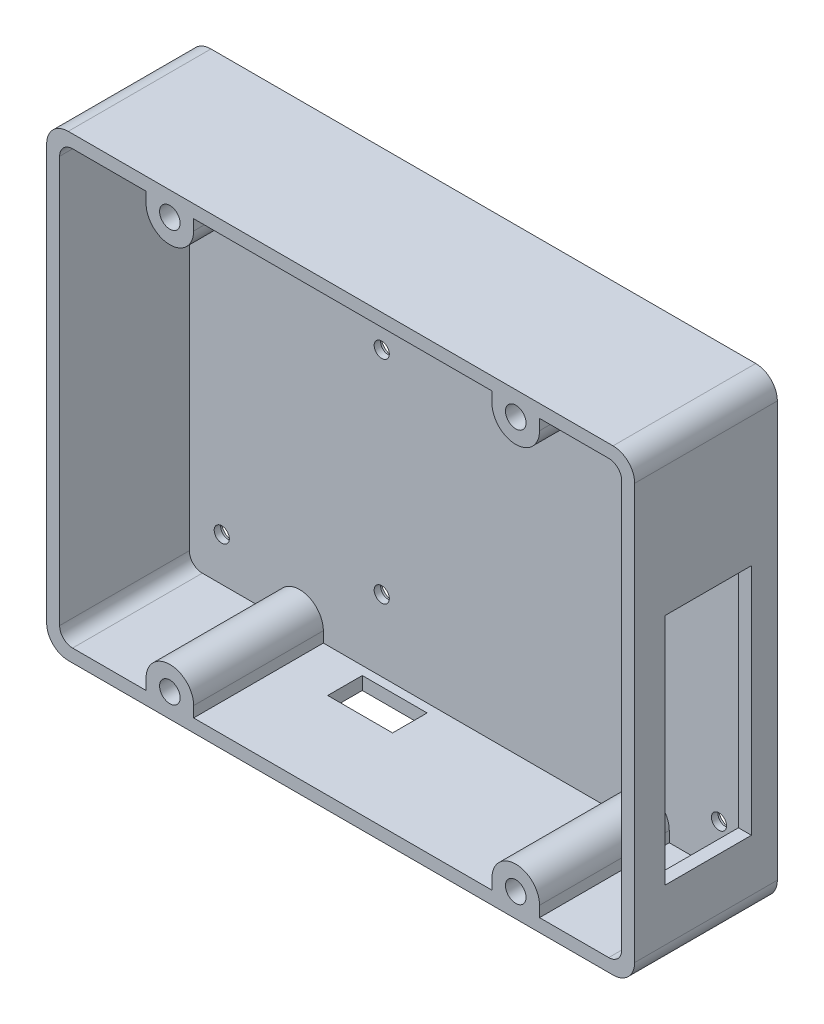
SolidWorks part; units mm, degrees
ref_plane "Plan de face" through (0, 0, 0) normal (0, 0, 1) x (1, 0, 0)
ref_plane "Plan de dessus" through (0, 0, 0) normal (0, 1, 0) x (1, 0, 0)
ref_plane "Plan de droite" through (0, 0, 0) normal (1, 0, 0) x (0, 0, -1)
sketch "Esquisse1" plane through (0, 0, 0) normal (0, 0, 1) x (1, 0, 0)
  line L0 (7.5, 10) -> (122.5, 10) construction
  line L1 (0, 0) -> (130, 0)
  line L2 (0, 0) -> (0, 100)
  line L3 (0, 100) -> (130, 100)
  line L4 (130, 0) -> (130, 100)
  line L5 (122.5, 10) -> (122.5, 94) construction
  line L6 (122.5, 94) -> (7.5, 94) construction
  line L7 (7.5, 94) -> (7.5, 10) construction
  line L8 (65, 40.971) -> (65, 68.9984) construction
  line L9 (44.5, 16.5) -> (102, 16.5) construction
  line L10 (102, 16.5) -> (102, 65.5) construction
  line L11 (102, 65.5) -> (44.5, 65.5) construction
  line L12 (44.5, 65.5) -> (44.5, 16.5) construction
  circle A0 centre (122.5, 10) radius 1.75
  circle A1 centre (122.5, 94) radius 1.75
  circle A2 centre (7.5, 94) radius 1.75
  circle A3 centre (7.5, 10) radius 1.75
  circle A4 centre (44.5, 65.5) radius 1.75
  circle A5 centre (102, 65.5) radius 1.75
  circle A6 centre (102, 16.5) radius 1.75
  circle A7 centre (44.5, 16.5) radius 1.75
  dimension "D5" = 3.5
  dimension "D1" = 100
  dimension "D2" = 130
  dimension "D3" = 115
  dimension "D4" = 84
  dimension "D6" = 6
  dimension "D7" = 57.5
  dimension "D8" = 49
  dimension "D9" = 20.5
  dimension "D10" = 6.5
extrude "Boss.-Extru.1" add sketch "Esquisse1" along normal blind 3
sketch "Esquisse2" plane through (0, 0, 0) normal (0, 0, -1) x (-1, 0, 0)
  circle A0 centre (-102, 16.5) radius 3.25
  circle A1 centre (-122.5, 10) radius 3.25
  circle A2 centre (-122.5, 94) radius 3.25
  circle A3 centre (-102, 65.5) radius 3.25
  circle A4 centre (-44.5, 65.5) radius 3.25
  circle A5 centre (-44.5, 16.5) radius 3.25
  circle A6 centre (-7.5, 10) radius 3.25
  circle A7 centre (-7.5, 94) radius 3.25
  dimension "D1" = 6.5
extrude "Enlèv. mat.-Extru.1" cut sketch "Esquisse2" against normal blind 1.5
sketch "Esquisse3" plane through (0, 0, 0) normal (0, 0, -1) x (-1, 0, 0)
  line L0 (0, 0) -> (0, -3) construction
  line L1 (0, 100) -> (-130, 100)
  line L2 (0, 100) -> (0, 0)
  line L3 (0, 0) -> (-130, 0)
  line L4 (-130, 100) -> (-130, 0)
  line L5 (3, 103) -> (-133, 103)
  line L6 (3, 103) -> (3, -3)
  line L7 (3, -3) -> (-133, -3)
  line L8 (-133, 103) -> (-133, -3)
  line L9 (0, 0) -> (3, 0) construction
  line L10 (-130, 100) -> (-130, 103) construction
  line L11 (-130, 100) -> (-133, 100) construction
  dimension "D1" = 3
extrude "Boss.-Extru.2" add sketch "Esquisse3" against normal blind 33
fillet "Congé1" radius 3 4 edges at (130, 0, 18) (0, 0, 18) (0, 100, 18) (130, 100, 18)
fillet "Congé2" radius 5 4 edges at (-3, -3, 16.5) (133, -3, 16.5) (133, 103, 16.5) (-3, 103, 16.5)
sketch "Esquisse4" plane through (130, 0, 0) normal (-1, 0, 0) x (0, 0, 1)
  line L0 (3, 3) -> (3, 97) construction
  line L1 (6, 14) -> (26, 14)
  line L2 (6, 14) -> (6, 68)
  line L3 (6, 68) -> (26, 68)
  line L4 (26, 14) -> (26, 68)
  line L5 (33, 0) -> (3, 0) construction
  dimension "D1" = 54
  dimension "D2" = 20
  dimension "D3" = 3
  dimension "D4" = 14
extrude "Enlèv. mat.-Extru.2" cut sketch "Esquisse4" against normal up to surface (3 mm away) up to face at (133, 50, 16.5)
sketch "Esquisse5" plane through (0, 0, 0) normal (0, 1, 0) x (1, 0, 0)
  line L0 (3, -3) -> (127, -3) construction
  line L1 (42, -5) -> (57, -5)
  line L2 (42, -5) -> (42, -13)
  line L3 (42, -13) -> (57, -13)
  line L4 (57, -5) -> (57, -13)
  line L7 (0, -33) -> (0, -3) construction
  dimension "D1" = 15
  dimension "D2" = 8
  dimension "D3" = 2
  dimension "D4" = 42
extrude "Enlèv. mat.-Extru.3" cut sketch "Esquisse5" against normal up to surface (3 mm away) up to face at (65, -3, 16.5)
sketch "Esquisse6" plane through (0, 0, 3) normal (0, 0, 1) x (1, 0, 0)
  line L0 (20, 97.525) -> (20, 100)
  line L1 (127, 100) -> (3, 100) construction
  line L2 (20, 100) -> (31, 100)
  line L3 (31, 100) -> (31, 97.525)
  line L4 (0, 97) -> (0, 3) construction
  line L5 (27.9696, 99.9) -> (32.8416, 99.9) construction
  line L6 (31, 2.475) -> (31, 0)
  line L7 (31, 0) -> (20, 0)
  line L8 (20, 0) -> (20, 2.475)
  line L9 (27.2118, 0.1) -> (22.3397, 0.1) construction
  line L10 (3, 0) -> (127, 0) construction
  arc A0 (20, 97.525) -> (31, 97.525) centre (25.5, 97.525) ccw
  circle A1 centre (25.5, 97.525) radius 2.375
  arc A2 (31, 2.475) -> (20, 2.475) centre (25.5, 2.475) ccw
  circle A3 centre (25.5, 2.475) radius 2.375
  dimension "D2" = 4.75
  dimension "D6" = 4.75
  dimension "D1" = 11
  dimension "D3" = 20
  dimension "D4" = 0.1
  dimension "D5" = 11
  dimension "D7" = 0.1
extrude "Boss.-Extru.3" add sketch "Esquisse6" along normal up to surface (30 mm away) up to face at (65, 50, 33)
pattern_linear "Répétition linéaire1" count 2 spacing 80 along (1, 0, 0) of "Boss.-Extru.3"
